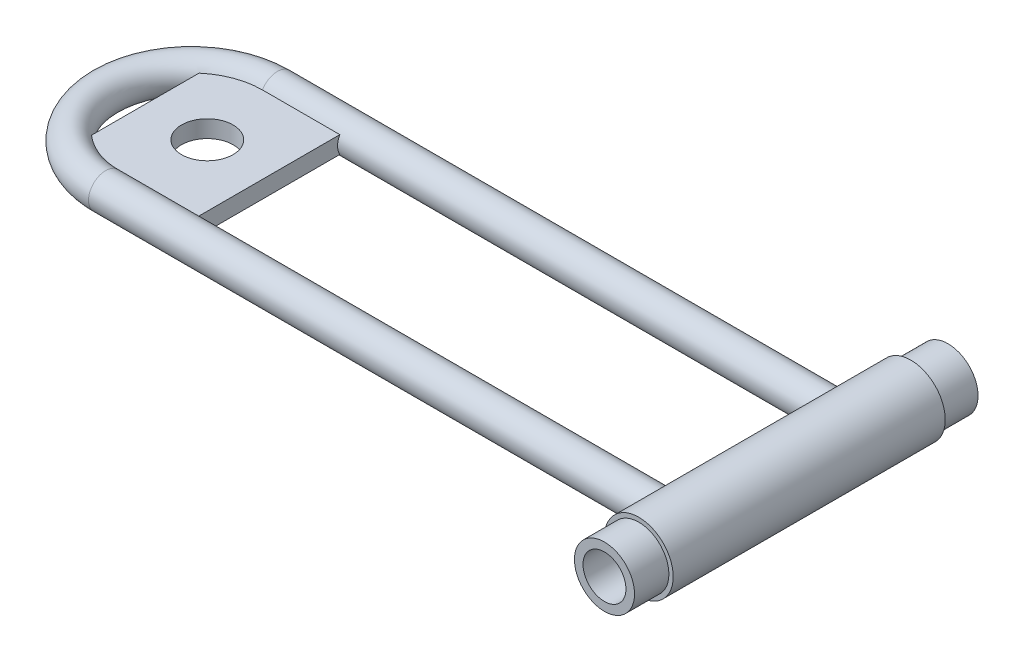
SolidWorks part; units mm, degrees
material "Cast Carbon Steel"
ref_plane "Front Plane" through (0, 0, 0) normal (0, 0, 1) x (1, 0, 0)
ref_plane "Top Plane" through (0, 0, 0) normal (0, 1, 0) x (1, 0, 0)
ref_plane "Right Plane" through (0, 0, 0) normal (1, 0, 0) x (0, 0, -1)
sketch "Sketch1" plane through (0, 0, 0) normal (0, 0, 1) x (1, 0, 0)
  circle A0 centre (0, 0) radius 6.35
  circle A1 centre (0, 0) radius 3.175
  dimension "D1" = 12.7
  dimension "D2" = 3.175
extrude "Boss-Extrude1" add sketch "Sketch1" along normal blind 62.992
ref_plane "Plane1" through (-3.81, 0, 0) normal (-1, 0, 0) x (0, 0, 1)
sketch "Sketch3" plane through (-3.81, 0, 0) normal (-1, 0, 0) x (0, 0, 1)
  line L0 (0, 0) -> (62.992, 0)
  line L1 (62.992, -6.35) -> (62.992, 6.35) construction
  circle A0 centre (-15.748, 0) radius 3.175
  circle A1 centre (47.244, 0) radius 3.175
  dimension "D3" = 6.35
  dimension "D4" = 6.35
  dimension "D1" = 15.748
  dimension "D2" = 15.748
sketch "Sketch4" plane through (0, 0, 0) normal (0, 1, 0) x (1, 0, 0)
  line L0 (-3.81, -15.6639) -> (-107.95, -15.6639)
  line L1 (-3.81, 0) -> (-3.81, -62.992) construction
  line L2 (-3.81, -47.0944) -> (-107.95, -47.0944)
  line L3 (-6.35, 0) -> (-6.35, -62.992) construction
  arc A0 (-107.95, -15.6639) -> (-107.95, -47.0944) centre (-107.95, -31.3792) ccw
  dimension "D1" = 101.6
  dimension "D2" = 15.7152
  dimension "D3" = 31.3792
sweep "Sweep1" add profiles "Sketch3" path "Sketch4"
ref_plane "Plane2" through (0, 0, 15.24) normal (0, 0, 1) x (1, 0, 0)
sketch "Sketch6" plane through (0, 0, 15.24) normal (0, 0, 1) x (1, 0, 0)
  line L0 (-116.5013, 0) -> (-93.6413, 0)
  line L3 (-93.6413, 0) -> (-116.5013, 0)
  line L4 (-93.6413, 0) -> (-93.6413, -1.5875)
  line L5 (-93.6413, -1.5875) -> (-116.5013, -1.5875)
  line L6 (-116.5013, 0) -> (-116.5013, -1.5875)
  line L7 (-93.6413, 0) -> (-116.5013, 0)
  line L8 (-93.6413, 0) -> (-93.6413, 1.5875)
  line L9 (-93.6413, 1.5875) -> (-116.5013, 1.5875)
  line L10 (-116.5013, 0) -> (-116.5013, 1.5875)
  circle A0 centre (0, 0) radius 3.175 construction
  point P3 (-105.0713, 0)
  dimension "D4" = 93.6413
  dimension "D1" = 22.86
  dimension "D2" = 1.5875
  dimension "D3" = 1.5875
extrude "Boss-Extrude3" add sketch "Sketch6" along normal blind 29.21 contours L0 L6 L5 L4 | L10 L0 L8 L9
sketch "Sketch7" plane through (0, 1.5875, 0) normal (0, 1, 0) x (1, 0, 0)
  line L1 (-93.6413, -44.45) -> (-93.6413, -18.2639) construction
  circle A0 centre (-105.0713, -31.3411) radius 4.7625
  dimension "D3" = 9.525
  dimension "D1" = 11.43
  dimension "D2" = 9.906
extrude "Cut-Extrude1" cut sketch "Sketch7" against normal blind 29.21
sketch "Sketch9" plane through (0, 0, 0) normal (0, 0, -1) x (-1, 0, 0)
  circle A0 centre (0, 0) radius 6.35
  circle A1 centre (0, 0) radius 3.175
  circle A2 centre (0, 0) radius 6.35 construction
  dimension "D1" = 6.35
  dimension "D2" = 12.7
ref_plane "Plane3" through (0, 0, 31.496) normal (0, 0, 1) x (1, 0, 0)
extrude "Boss-Extrude5" add sketch "Sketch9" along normal blind 6.35
mirror "Mirror1" about plane through (0, 0, 31.496) normal (0, 0, 1) of "Boss-Extrude5"
sketch "Sketch10" plane through (0, 0, 69.342) normal (0, 0, 1) x (1, 0, 0)
  circle A0 centre (0, 0) radius 5.5562
  circle A1 centre (0, 0) radius 6.35
  dimension "D1" = 11.1125
  dimension "D2" = 12.7
extrude "Cut-Extrude6" cut sketch "Sketch10" against normal blind 12.7
sketch "Sketch12" plane through (0, 0, -6.35) normal (0, 0, -1) x (-1, 0, 0)
  circle A0 centre (0, 0) radius 5.5562
  circle A1 centre (0, 0) radius 6.35
  circle A2 centre (0, 0) radius 6.35 construction
  dimension "D1" = 11.1125
  dimension "D2" = 12.7
extrude "Cut-Extrude7" cut sketch "Sketch12" against normal blind 12.7
sketch "Sketch13" plane through (0, 0, 69.342) normal (0, 0, 1) x (1, 0, 0)
  circle A0 centre (0, 0) radius 5.5563
  circle A1 centre (0, 0) radius 3.175
  circle A2 centre (0, 0) radius 3.175 construction
  dimension "D1" = 6.35
  dimension "D2" = 11.1125
extrude "Cut-Extrude8" cut sketch "Sketch13" against normal blind 6.35
sketch "Sketch14" plane through (0, 0, -6.35) normal (0, 0, -1) x (-1, 0, 0)
  circle A0 centre (0, 0) radius 5.5563
  circle A1 centre (0, 0) radius 3.175
  circle A2 centre (0, 0) radius 3.175 construction
  dimension "D1" = 6.35
  dimension "D2" = 11.1125
extrude "Cut-Extrude9" cut sketch "Sketch14" against normal blind 6.35
sketch "Sketch16" plane through (0, 0, 0) normal (0, 0, -1) x (-1, 0, 0)
  circle A0 centre (0, 0) radius 3.9688
  dimension "D1" = 7.9375
extrude "Cut-Extrude11" cut sketch "Sketch16" against normal through all
sketch "Sketch18" plane through (0, 0, 0) normal (0, 0, -1) x (-1, 0, 0)
  circle A0 centre (0, 0) radius 5.5563
  circle A1 centre (0, 0) radius 3.9688
  circle A2 centre (0, 0) radius 3.9688 construction
  dimension "D1" = 7.9375
  dimension "D2" = 11.1125
extrude "Boss-Extrude7" add sketch "Sketch18" along normal blind 0.508
